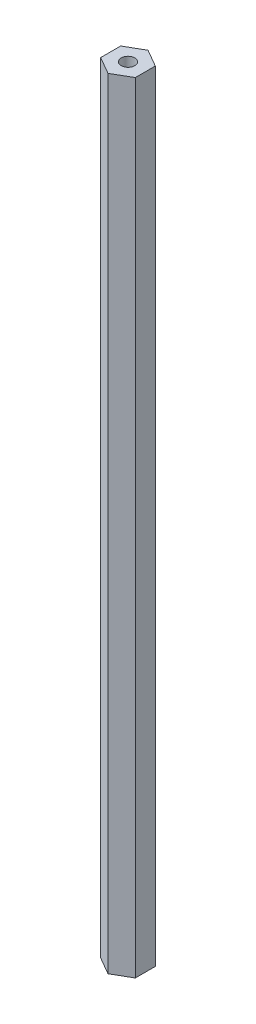
SolidWorks part; units mm, degrees
ref_plane "Front Plane" through (0, 0, 0) normal (0, 0, 1) x (1, 0, 0)
ref_plane "Top Plane" through (0, 0, 0) normal (0, 1, 0) x (1, 0, 0)
ref_plane "Right Plane" through (0, 0, 0) normal (1, 0, 0) x (0, 0, -1)
sketch "Sketch1" plane through (0, 0, 0) normal (0, 1, 0) x (1, 0, 0)
  line L1 (6.35, 3.6662) -> (0, 7.3323)
  line L2 (0, 7.3323) -> (-6.35, 3.6662)
  line L3 (-6.35, 3.6662) -> (-6.35, -3.6662)
  line L4 (-6.35, -3.6662) -> (0, -7.3323)
  line L5 (0, -7.3323) -> (6.35, -3.6662)
  line L6 (6.35, -3.6662) -> (6.35, 3.6662)
  circle A0 centre (0, 0) radius 6.35 construction
  dimension "D1" = 12.7
extrude "Boss-Extrude1" add sketch "Sketch1" along normal blind 285.75
sketch "Sketch2" plane through (0, 0, 0) normal (0, -1, 0) x (1, 0, 0)
  circle A0 centre (0, 0) radius 2.4892
  dimension "D1" = 4.9784
extrude "Cut-Extrude1" cut sketch "Sketch2" against normal blind 25.4
sketch "Sketch3" plane through (0, 285.75, 0) normal (0, 1, 0) x (1, 0, 0)
  circle A0 centre (0, 0) radius 2.4892
  dimension "D1" = 4.9784
extrude "Cut-Extrude2" cut sketch "Sketch3" against normal blind 25.4
